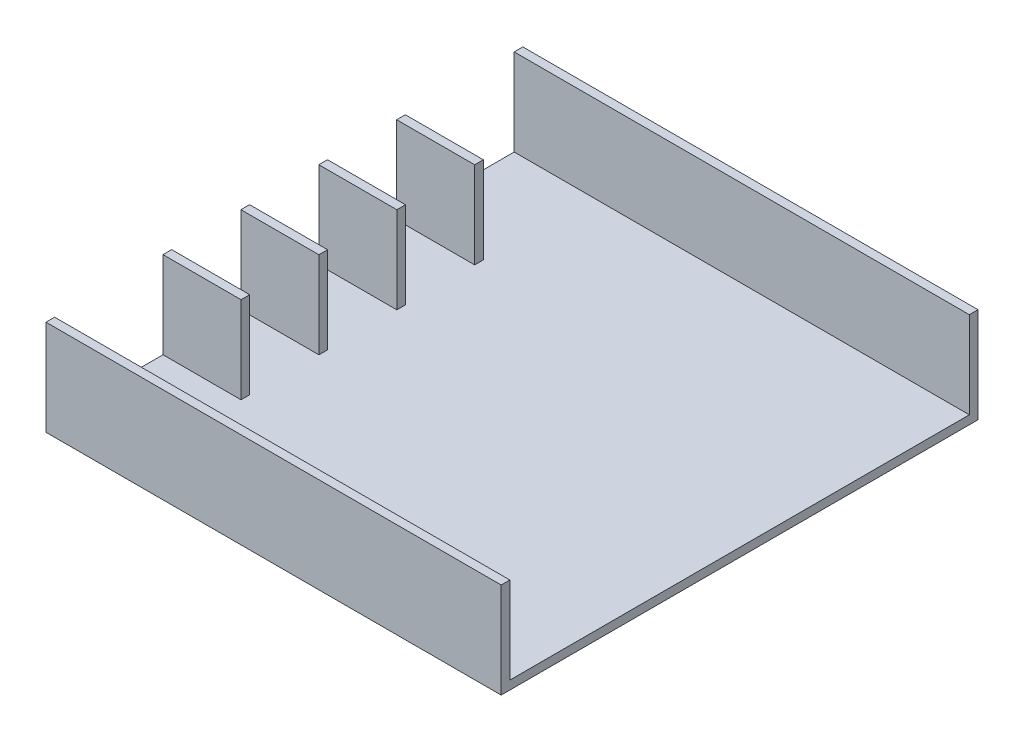
SolidWorks part; units mm, degrees
ref_plane "Front Plane" through (0, 0, 0) normal (0, 0, 1) x (1, 0, 0)
ref_plane "Top Plane" through (0, 0, 0) normal (0, 1, 0) x (1, 0, 0)
ref_plane "Right Plane" through (0, 0, 0) normal (1, 0, 0) x (0, 0, -1)
sketch "Sketch2" plane through (0, 0, 0) normal (0, 1, 0) x (1, 0, 0)
  line L1 (-52.5, 55) -> (52.5, 55)
  line L2 (-52.5, 55) -> (-52.5, -55)
  line L3 (-52.5, -55) -> (52.5, -55)
  line L4 (52.5, 55) -> (52.5, -55)
  line L5 (-52.5, 55) -> (52.5, -55) construction
  line L6 (-52.5, -55) -> (52.5, 55) construction
  point P0 (0, 0)
extrude "Boss-Extrude1" add sketch "Sketch2" along normal blind 2
sketch "Sketch4" plane through (0, 2, 0) normal (0, 1, 0) x (1, 0, 0)
  line L7 (-52.5, 55) -> (-52.5, -55) construction
  line L8 (-34.5, 25.8951) -> (-52.5, 25.8951)
  line L9 (-34.5, 25.8951) -> (-34.5, 27.8951)
  line L10 (-34.5, 27.8951) -> (-52.5, 27.8951)
  line L11 (-52.5, 25.8951) -> (-52.5, 27.8951)
  line L12 (-34.5, 25.8951) -> (-52.5, 27.8951) construction
  line L13 (-34.5, 27.8951) -> (-52.5, 25.8951) construction
  line L15 (-34.5, 7.9341) -> (-52.5, 7.9341)
  line L16 (-34.5, 7.9341) -> (-34.5, 9.9341)
  line L17 (-34.5, 9.9341) -> (-52.5, 9.9341)
  line L18 (-52.5, 7.9341) -> (-52.5, 9.9341)
  line L19 (-34.5, 7.9341) -> (-52.5, 9.9341) construction
  line L20 (-34.5, 9.9341) -> (-52.5, 7.9341) construction
  line L21 (-34.5, -10.0402) -> (-52.5, -10.0402)
  line L22 (-34.5, -10.0402) -> (-34.5, -8.0402)
  line L23 (-34.5, -8.0402) -> (-52.5, -8.0402)
  line L24 (-52.5, -10.0402) -> (-52.5, -8.0402)
  line L25 (-34.5, -10.0402) -> (-52.5, -8.0402) construction
  line L26 (-34.5, -8.0402) -> (-52.5, -10.0402) construction
  line L27 (-34.5, -28.0064) -> (-52.5, -28.0064)
  line L28 (-34.5, -28.0064) -> (-34.5, -26.0064)
  line L29 (-34.5, -26.0064) -> (-52.5, -26.0064)
  line L30 (-52.5, -28.0064) -> (-52.5, -26.0064)
  line L31 (-34.5, -28.0064) -> (-52.5, -26.0064) construction
  line L32 (-34.5, -26.0064) -> (-52.5, -28.0064) construction
  line L33 (-52.5, 55) -> (52.5, 55)
  line L34 (-52.5, 55) -> (-52.5, 53)
  line L35 (-52.5, 53) -> (52.5, 53)
  line L36 (52.5, 55) -> (52.5, 53)
  line L37 (-52.5, -55) -> (52.5, -55)
  line L38 (-52.5, -55) -> (-52.5, -53)
  line L39 (-52.5, -53) -> (52.5, -53)
  line L40 (52.5, -55) -> (52.5, -53)
extrude "Boss-Extrude2" add sketch "Sketch4" along normal blind 20
sketch "Sketch5"
